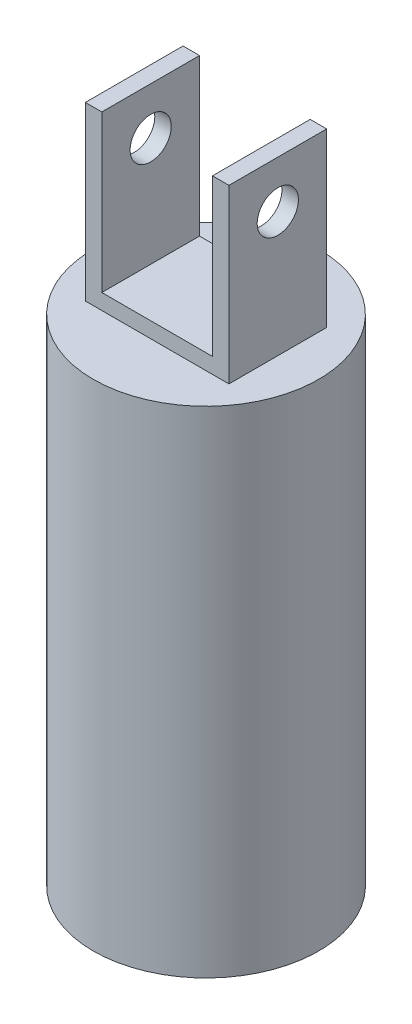
SolidWorks part; units mm, degrees
material "PBT General Purpose"
ref_plane "Front Plane" through (0, 0, 0) normal (0, 0, 1) x (1, 0, 0)
ref_plane "Top Plane" through (0, 0, 0) normal (0, 1, 0) x (1, 0, 0)
ref_plane "Right Plane" through (0, 0, 0) normal (1, 0, 0) x (0, 0, -1)
sketch "Sketch1" plane through (0, 0, 0) normal (0, 0, 1) x (1, 0, 0)
  line L0 (21.0312, 0) -> (21.0312, 4.572)
  line L1 (0, 0) -> (42.0624, 0)
  line L2 (0, 0) -> (0, 50.3809)
  line L3 (0, 50.3809) -> (4.826, 50.3809)
  line L4 (42.0624, 0) -> (42.0624, 50.3809)
  line L5 (42.0624, 24.8065) -> (37.2364, 24.8065)
  line L6 (0, 25.1904) -> (4.826, 25.1904)
  line L7 (4.826, 25.1904) -> (4.826, 50.3809)
  line L8 (37.2364, 24.8065) -> (37.2364, 50.3809)
  line L9 (37.2364, 50.3809) -> (42.0624, 50.3809)
  line L11 (4.826, 25.1904) -> (4.826, 4.572)
  line L12 (4.826, 4.572) -> (37.2364, 4.572)
  line L13 (37.2364, 25.1904) -> (37.2364, 4.572)
  dimension "D1" = 42.0624
  dimension "D2" = 50.3809
  dimension "D3" = 4.572
  dimension "D4" = 4.826
  dimension "D5" = 4.826
extrude "Boss-Extrude1" add sketch "Sketch1" along normal blind 28.6258 contours L9 L8 L5 L4 | L5 L13 L12 L0 L1 L4 | L12 L11 L6 L2 L1 L0 | L6 L7 L3 L2
sketch "Sketch2" plane through (0, 0, 0) normal (0, -1, 0) x (1, 0, 0)
  circle A0 centre (21.0312, 14.3129) radius 25.4
  dimension "D1" = 50.8
extrude "Boss-Extrude2" add sketch "Sketch2" along normal blind 145.034
sketch "Sketch4" plane through (0, 0, 0) normal (0, 1, 0) x (1, 0, 0)
  circle A0 centre (21.0312, -14.3129) radius 33.02
  dimension "D1" = 66.04
extrude "Boss-Extrude3" add sketch "Sketch4" against normal up to surface (145.034 mm away) up to face at (21.0312, -145.034, -11.0871)
sketch "Sketch5" plane through (42.0624, 0, 0) normal (1, 0, 0) x (0, 0, -1)
  line L0 (-14.3129, -145.034) -> (-14.3129, 36.576)
  line L1 (-28.6258, -145.034) -> (0, -145.034) construction
  line L3 (-28.6258, 50.3809) -> (0, 50.3809) construction
  circle A0 centre (-14.3129, 36.576) radius 6.0325
  dimension "D2" = 12.065
  dimension "D1" = 13.8049
extrude "Cut-Extrude2" cut sketch "Sketch5" against normal through all
sketch "Sketch6" plane through (0, -145.034, 0) normal (0, -1, 0) x (1, 0, 0)
  circle A0 centre (21.0312, 14.3129) radius 19.812
  dimension "D1" = 39.624
extrude "Cut-Extrude3" cut sketch "Sketch6" against normal blind 106.934
